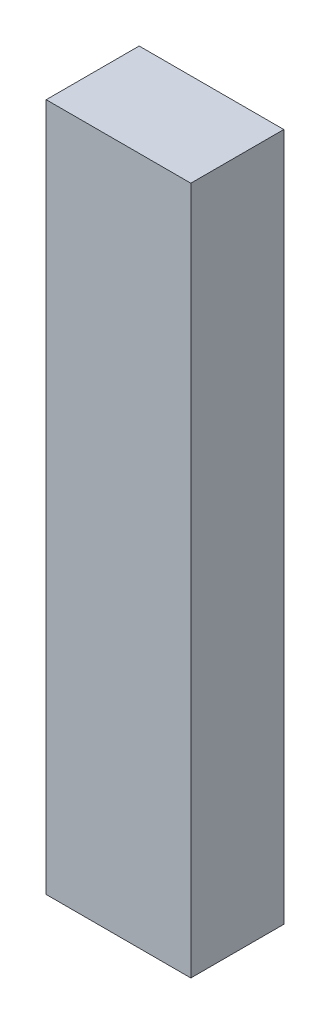
SolidWorks part; units mm, degrees
ref_plane "Front Plane" through (0, 0, 0) normal (0, 0, 1) x (1, 0, 0)
ref_plane "Top Plane" through (0, 0, 0) normal (0, 1, 0) x (1, 0, 0)
ref_plane "Right Plane" through (0, 0, 0) normal (1, 0, 0) x (0, 0, -1)
sketch "Sketch1" plane through (0, 0, 0) normal (0, 1, 0) x (1, 0, 0)
  line L1 (-35, 22.5) -> (35, 22.5)
  line L2 (-35, 22.5) -> (-35, -22.5)
  line L3 (-35, -22.5) -> (35, -22.5)
  line L4 (35, 22.5) -> (35, -22.5)
  line L5 (-35, 22.5) -> (35, -22.5) construction
  line L6 (-35, -22.5) -> (35, 22.5) construction
  point P0 (0, 0)
  dimension "D1" = 45
  dimension "D2" = 70
extrude "Shape" add sketch "Sketch1" along normal blind 1000
sketch "Sketch2" [suppressed] plane through (0, 0, 22.5) normal (0, 0, 1) x (1, 0, 0)
  line L0 (-35, 400) -> (35, 330)
  line L1 (35, 400) -> (35, 0) construction
  line L2 (-35, 400) -> (35, 400) construction
  line L3 (35, 200) -> (-35, 200) construction
  line L4 (-35, 0) -> (35, 70)
  line L7 (-35, 0) -> (35, 0)
  line L8 (35, 0) -> (35, 400)
  line L9 (35, 400) -> (-35, 400)
  line L10 (-35, 400) -> (-35, 0)
  line L11 (-35, 0) -> (35, 0)
  line L12 (35, 0) -> (35, 400)
  line L13 (35, 400) -> (-35, 400)
  line L14 (-35, 400) -> (-35, 0)
  dimension "D1" = 45
  dimension "D2" = 0
extrude "Merger cut" [suppressed] cut sketch "Sketch2" against normal up to next
sketch "Sketch3" [suppressed] plane through (0, 0, 22.5) normal (0, 0, 1) x (1, 0, 0)
  line L0 (149.47, 940.7422) -> (-8.672, 826.654) construction
  line L1 (149.47, 940.7422) -> (-8.672, 826.654)
  line L2 (-35, 863.1483) -> (123.142, 977.2365) construction
  line L3 (-35, 863.1483) -> (123.142, 977.2365)
  line L4 (-8.672, 826.654) -> (751.9158, -227.626) construction
  line L5 (-8.672, 826.654) -> (751.9158, -227.626)
  line L6 (-8.672, 826.654) -> (-35, 863.1483) construction
  line L7 (-8.672, 826.654) -> (-35, 863.1483)
  line L8 (775.9846, 585.0675) -> (-35, 0) construction
  line L9 (775.9846, 585.0675) -> (-35, 0)
  line L10 (-35, 0) -> (35, 0)
  line L11 (35, 0) -> (35, 1000)
  line L12 (35, 1000) -> (-35, 1000)
  line L13 (-35, 1000) -> (-35, 0)
  line L14 (-35, 0) -> (35, 0)
  line L15 (35, 0) -> (35, 1000)
  line L16 (35, 1000) -> (-35, 1000)
  line L17 (-35, 1000) -> (-35, 0)
  dimension "D1" = 0
extrude "Front diagonal cut" [suppressed] cut sketch "Sketch3" against normal up to next
sketch "Sketch4" [suppressed] plane through (0, 0, 22.5) normal (0, 0, 1) x (1, 0, 0)
  line L0 (884.145, 393.9193) -> (-35, 0) construction
  line L1 (884.145, 393.9193) -> (-35, 0)
  line L2 (144.2333, 838.3916) -> (-35, 761.5773) construction
  line L3 (144.2333, 838.3916) -> (-35, 761.5773)
  line L4 (-35, 761.5773) -> (-17.2736, 720.2158) construction
  line L5 (-35, 761.5773) -> (-17.2736, 720.2158)
  line L6 (-35, 0) -> (35, 0)
  line L7 (35, 0) -> (35, 1000)
  line L8 (35, 1000) -> (-35, 1000)
  line L9 (-35, 1000) -> (-35, 0)
  line L10 (-35, 0) -> (35, 0)
  line L11 (35, 0) -> (35, 1000)
  line L12 (35, 1000) -> (-35, 1000)
  line L13 (-35, 1000) -> (-35, 0)
  line L14 (494.8215, -474.6728) -> (-17.2736, 720.2158) construction
  line L15 (494.8215, -474.6728) -> (-17.2736, 720.2158)
  line L16 (161.9596, 797.03) -> (-17.2736, 720.2158) construction
  line L17 (161.9596, 797.03) -> (-17.2736, 720.2158)
  dimension "D1" = 0
extrude "Cut-Extrude1" [suppressed] cut sketch "Sketch4" against normal up to next
ref_plane "Plane1" through (35, 666.8517, 22.5) normal (1, 0, 0) x (0, 0, -1)
sketch "Sketch6" plane through (0, 0, 22.5) normal (0, 0, 1) x (1, 0, 0)
  line L0 (-645, 666.8517) -> (35, 666.8517) construction
  line L1 (-645, 666.8517) -> (35, 666.8517)
  line M1 (-35, 0) -> (35, 0)
  line M2 (35, 0) -> (35, 1000)
  line M4 (-35, 1000) -> (-35, 0)
extrude "Cut-Extrude2" cut sketch "Sketch6" against normal through all and the other way through all contours L1 M4 M1 M2
